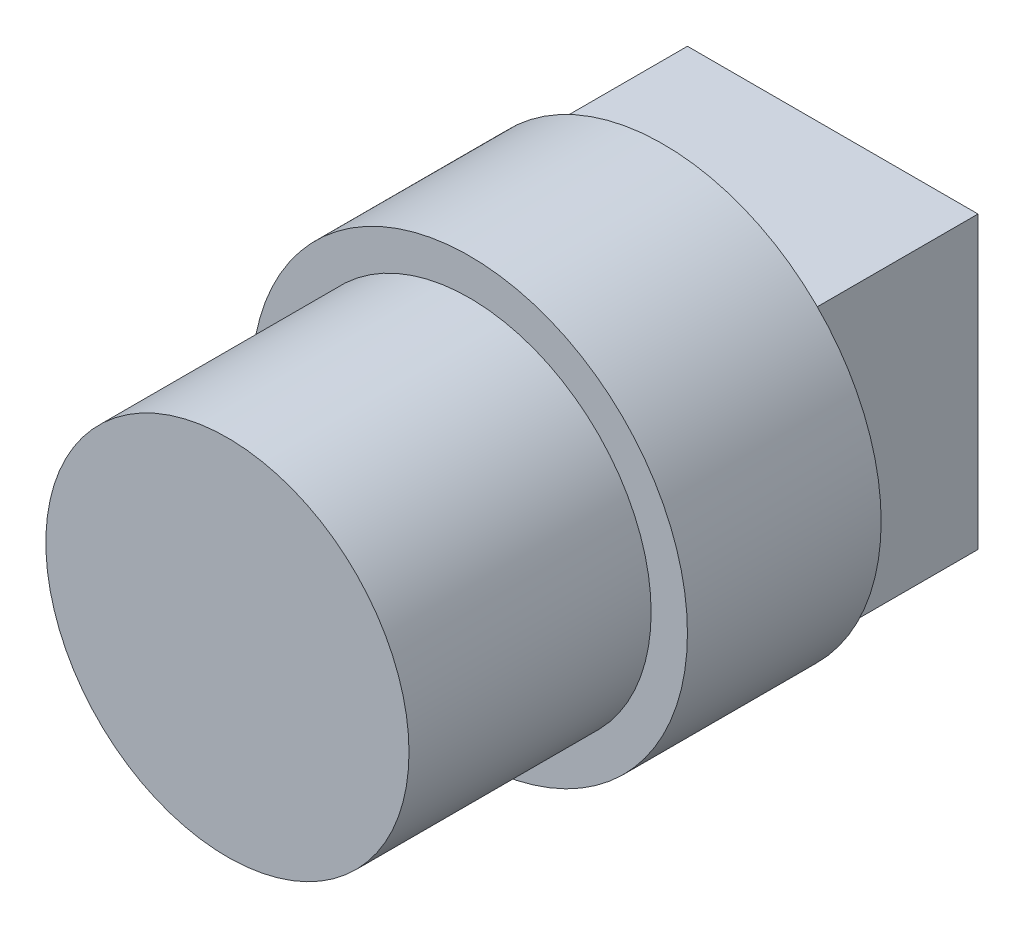
SolidWorks part; units mm, degrees
ref_plane "Alzado" through (0, 0, 0) normal (0, 0, 1) x (1, 0, 0)
ref_plane "Planta" through (0, 0, 0) normal (0, 1, 0) x (1, 0, 0)
ref_plane "Vista lateral" through (0, 0, 0) normal (1, 0, 0) x (0, 0, -1)
sketch "Croquis1" plane through (0, 0, 0) normal (0, 0, 1) x (1, 0, 0)
  line L1 (-3, -3) -> (3, -3)
  line L2 (-3, -3) -> (-3, 3)
  line L3 (-3, 3) -> (3, 3)
  line L4 (3, -3) -> (3, 3)
  line L5 (-3, -3) -> (3, 3) construction
  line L6 (-3, 3) -> (3, -3) construction
  point P0 (0, 0)
  dimension "D1" = 6
  dimension "D2" = 6
extrude "Saliente-Extruir1" add sketch "Croquis1" along normal blind 3.5
sketch "Croquis2" plane through (0, 0, 3.5) normal (0, 0, 1) x (1, 0, 0)
  circle A0 centre (0, 0) radius 4.5
  dimension "D1" = 9
extrude "Saliente-Extruir2" add sketch "Croquis2" along normal blind 4
sketch "Croquis3" plane through (0, 0, 7.5) normal (0, 0, 1) x (1, 0, 0)
  circle A0 centre (0, 0) radius 3.75
  dimension "D1" = 7.5
extrude "Saliente-Extruir3" add sketch "Croquis3" along normal blind 5
ref_plane "Plano1" through (0, 0, 0) normal (1, 0, 0) x (0, 0, -1)
